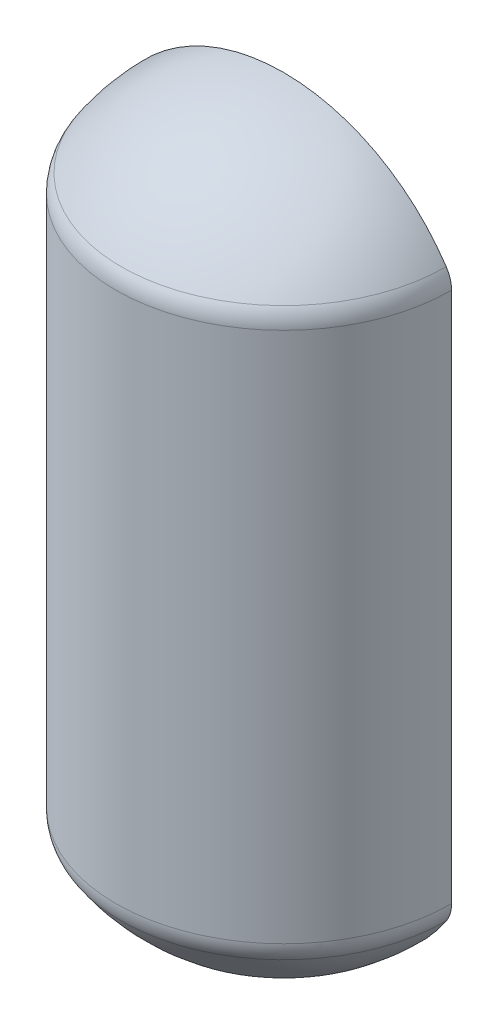
SolidWorks part; units mm, degrees
material "Custom Plastic"
ref_plane "Front Plane" through (0, 0, 0) normal (0, 0, 1) x (1, 0, 0)
ref_plane "Top Plane" through (0, 0, 0) normal (0, 1, 0) x (1, 0, 0)
ref_plane "Right Plane" through (0, 0, 0) normal (1, 0, 0) x (0, 0, -1)
sketch "Sketch1" plane through (0, 0, 0) normal (0, 0, 1) x (1, 0, 0)
  line L0 (0, 0) -> (0, 1200) construction
  line L1 (-133.985, 76.2) -> (133.985, 76.2) construction
  line L2 (-133.985, 0) -> (133.985, 0) construction
  line L3 (-133.985, 0) -> (-133.985, 1200) construction
  line L4 (-133.985, 1200) -> (133.985, 1200) construction
  line L5 (133.985, 0) -> (133.985, 1200) construction
  line L6 (-133.985, 0) -> (133.985, 1200) construction
  line L7 (-133.985, 1200) -> (133.985, 0) construction
  line L8 (-133.985, 685.1) -> (133.985, 685.1) construction
  line L9 (-133.985, 1123.8) -> (133.985, 1123.8) construction
  line L10 (-133.985, 608.9) -> (133.985, 608.9) construction
  line L11 (-133.985, 532.7) -> (133.985, 532.7) construction
  line L12 (-133.985, 608.9) -> (0, 608.9) construction
  line L13 (0, 608.9) -> (133.985, 608.9) construction
  line L14 (-133.985, 1123.8) -> (-133.985, 685.1)
  line L15 (133.985, 1123.8) -> (133.985, 685.1) construction
  line L16 (-133.985, 532.7) -> (-133.985, 76.2)
  line L17 (133.985, 532.7) -> (133.985, 76.2) construction
  line L18 (-130.81, 531.8223) -> (-130.81, 77.0777)
  line L19 (130.81, 531.8223) -> (130.81, 77.0777) construction
  line L20 (-130.81, 1122.9223) -> (-130.81, 685.9777)
  line L21 (130.81, 1122.9223) -> (130.81, 685.9777) construction
  line L22 (0, 3.175) -> (0, 0)
  line L23 (0, 605.725) -> (0, 608.9)
  line L24 (0, 612.075) -> (0, 608.9)
  line L25 (0, 1200) -> (0, 1196.825)
  line L26 (0, 1200) -> (0, 0)
  arc A0 (0, 0) -> (-133.985, 76.2) centre (0, 155.8951) cw
  arc A1 (0, 0) -> (133.985, 76.2) centre (0, 155.8951) ccw construction
  arc A2 (0, 1200) -> (133.985, 1123.8) centre (0, 1044.1049) cw construction
  arc A3 (0, 1200) -> (-133.985, 1123.8) centre (0, 1044.1049) ccw
  arc A4 (0, 608.9) -> (-133.985, 532.7) centre (0, 453.0049) ccw
  arc A5 (0, 608.9) -> (133.985, 532.7) centre (0, 453.0049) cw construction
  arc A6 (0, 608.9) -> (-133.985, 685.1) centre (0, 764.7951) cw
  arc A7 (0, 608.9) -> (133.985, 685.1) centre (0, 764.7951) ccw construction
  arc A8 (0, 605.725) -> (-130.81, 531.8223) centre (0, 453.0049) ccw
  arc A9 (0, 3.175) -> (-130.81, 77.0777) centre (0, 155.8951) cw
  arc A10 (0, 3.175) -> (130.81, 77.0777) centre (0, 155.8951) ccw construction
  arc A11 (0, 605.725) -> (130.81, 531.8223) centre (0, 453.0049) cw construction
  arc A12 (0, 612.075) -> (-130.81, 685.9777) centre (0, 764.7951) cw
  arc A13 (0, 1196.825) -> (-130.81, 1122.9223) centre (0, 1044.1049) ccw
  arc A14 (0, 1196.825) -> (130.81, 1122.9223) centre (0, 1044.1049) cw construction
  arc A15 (0, 612.075) -> (130.81, 685.9777) centre (0, 764.7951) ccw construction
  point P3 (0, 600)
  dimension "D3" = 76.2
  dimension "D1" = 1200
  dimension "D2" = 267.97
  dimension "D4" = 76.2
  dimension "D5" = 76.2
  dimension "D6" = 1200
  dimension "D7" = 591.1
  dimension "D8" = 76.2
  dimension "D9" = 3.175
  dimension "D10" = 3.175
revolve "Revolve2" add sketch "Sketch1" angle 180 about L0
fillet "Fillet1" radius 25.4 2 edges at (0, 685.1, 133.985) (0, 1123.8, 133.985)
